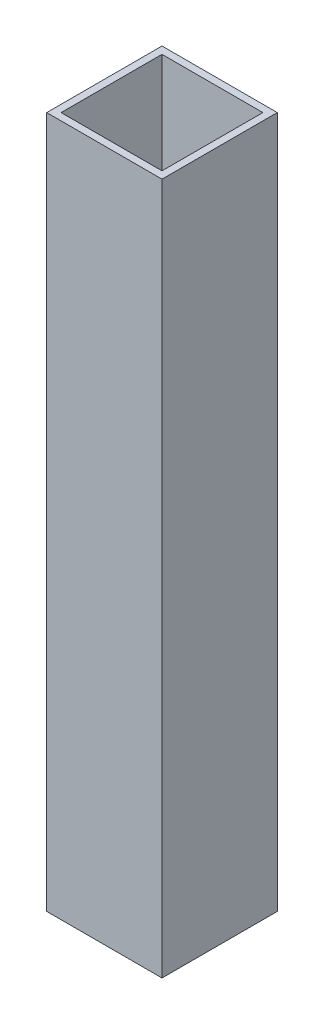
SolidWorks part; units mm, degrees
material "6061-T6 (SS)"
ref_plane "Front Plane" through (0, 0, 0) normal (0, 0, 1) x (1, 0, 0)
ref_plane "Top Plane" through (0, 0, 0) normal (0, 1, 0) x (1, 0, 0)
ref_plane "Right Plane" through (0, 0, 0) normal (1, 0, 0) x (0, 0, -1)
sketch "Sketch1" plane through (0, 0, 0) normal (0, 1, 0) x (1, 0, 0)
  line L0 (-11.1125, 11.1125) -> (-11.1125, -11.1125)
  line L1 (-12.7, 12.7) -> (12.7, 12.7)
  line L2 (-12.7, 12.7) -> (-12.7, -12.7)
  line L3 (-12.7, -12.7) -> (12.7, -12.7)
  line L4 (12.7, 12.7) -> (12.7, -12.7)
  line L5 (-12.7, 12.7) -> (12.7, -12.7) construction
  line L6 (-12.7, -12.7) -> (12.7, 12.7) construction
  line L7 (-11.1125, -11.1125) -> (11.1125, -11.1125)
  line L8 (11.1125, 11.1125) -> (11.1125, -11.1125)
  line L9 (-11.1125, 11.1125) -> (11.1125, 11.1125)
  point P0 (0, 0)
  dimension "D1" = 25.4
  dimension "D2" = 25.4
  dimension "D3" = 1.5875
extrude "Boss-Extrude1" add sketch "Sketch1" along normal blind 152.4
